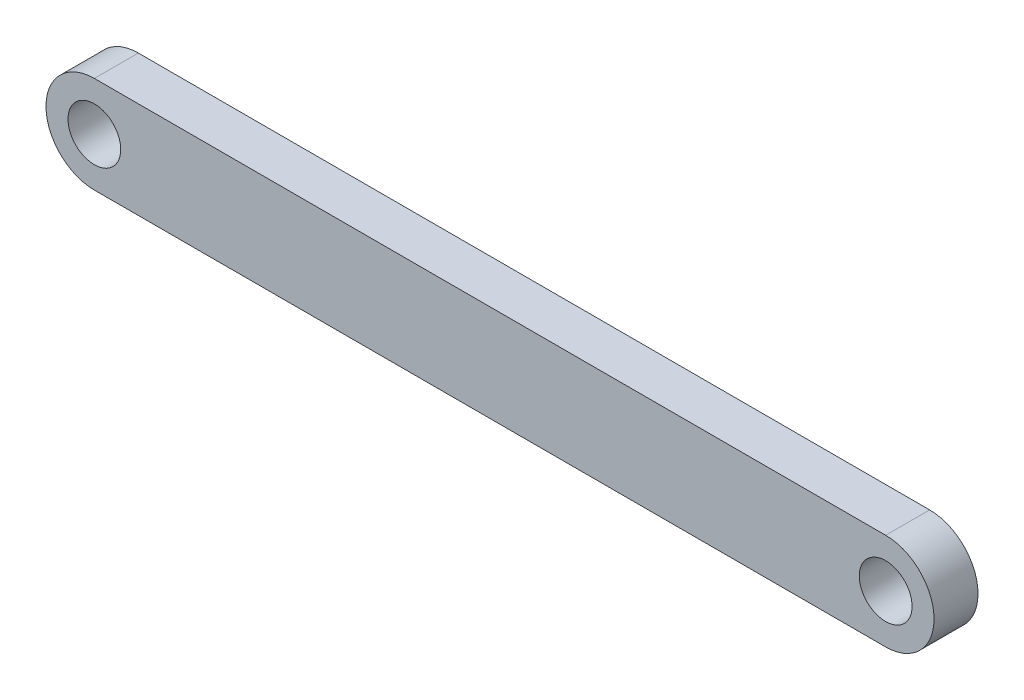
SolidWorks part; units mm, degrees
ref_plane "Front Plane" through (0, 0, 0) normal (0, 0, 1) x (1, 0, 0)
ref_plane "Top Plane" through (0, 0, 0) normal (0, 1, 0) x (1, 0, 0)
ref_plane "Right Plane" through (0, 0, 0) normal (1, 0, 0) x (0, 0, -1)
sketch "Sketch1" plane through (0, 0, 0) normal (0, 0, 1) x (1, 0, 0)
  line L0 (-45, 0) -> (45, 0) construction
  line L1 (-45, 5.5) -> (45, 5.5)
  line L2 (-45, -5.5) -> (45, -5.5)
  arc A0 (-45, 5.5) -> (-45, -5.5) centre (-45, 0) ccw
  arc A1 (45, -5.5) -> (45, 5.5) centre (45, 0) ccw
  circle A2 centre (-45, 0) radius 3
  circle A3 centre (45, 0) radius 3
  point P2 (0, 0)
  dimension "D3" = 6
  dimension "D1" = 11
  dimension "D2" = 90
extrude "Boss-Extrude1" add sketch "Sketch1" along normal mid plane 5
